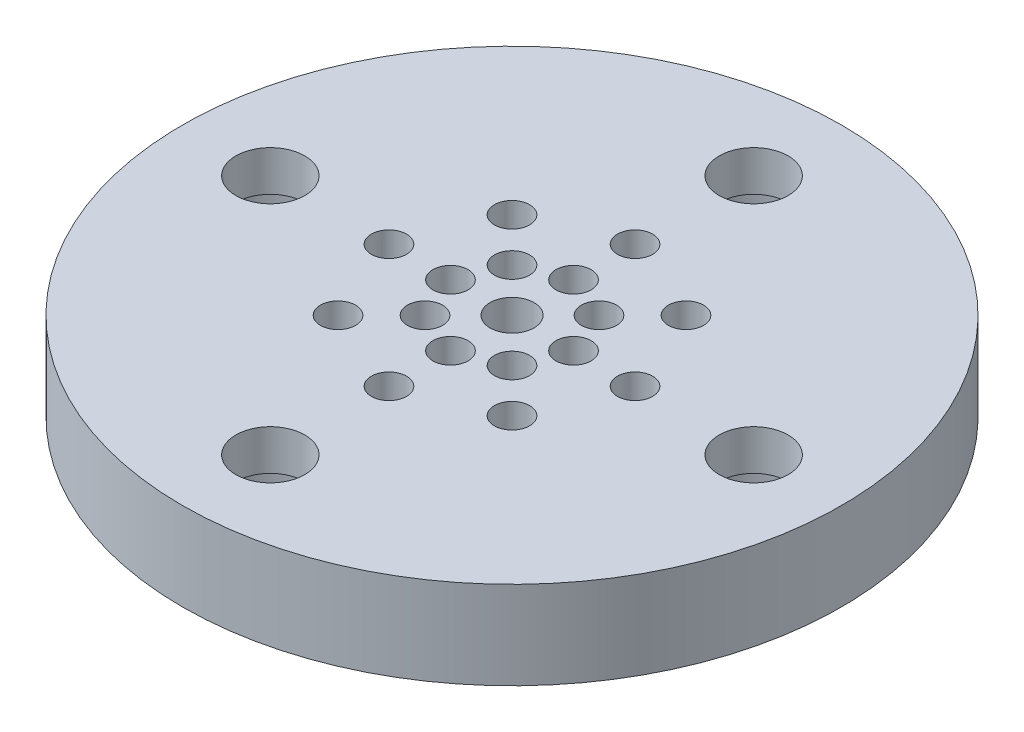
SolidWorks part; units mm, degrees
ref_plane "Front Plane" through (0, 0, 0) normal (0, 0, 1) x (1, 0, 0)
ref_plane "Top Plane" through (0, 0, 0) normal (0, 1, 0) x (1, 0, 0)
ref_plane "Right Plane" through (0, 0, 0) normal (1, 0, 0) x (0, 0, -1)
sketch "Sketch1" plane through (0, 0, 0) normal (0, 1, 0) x (1, 0, 0)
  circle A1 centre (0, 0) radius 50.8
  dimension "D1" = 101.6
extrude "Boss-Extrude1" add sketch "Sketch1" along normal blind 25.4
sketch "Sketch2" plane through (0, 0, 0) normal (0, -1, 0) x (1, 0, 0)
  circle A0 centre (0, 0) radius 50.8
  circle A1 centre (0, 0) radius 69.85
  dimension "D1" = 139.7
extrude "Boss-Extrude2" add sketch "Sketch2" against normal blind 12.7
sketch "Sketch3" plane through (0, 0, 0) normal (0, -1, 0) x (1, 0, 0)
  circle A0 centre (0, 0) radius 49.53
  circle A1 centre (0, 0) radius 47.625
  dimension "D1" = 99.06
  dimension "D2" = 95.25
extrude "Cut-Extrude1" cut sketch "Sketch3" against normal blind 1.1176
sketch "Sketch4" plane through (0, 0, 0) normal (0, -1, 0) x (1, 0, 0)
  circle A0 centre (0, -59.9186) radius 3.175
  circle A1 centre (-42.3688, -42.3688) radius 3.175
  circle A2 centre (-59.9186, 0) radius 3.175
  circle A3 centre (-42.3688, 42.3688) radius 3.175
  circle A4 centre (0, 59.9186) radius 3.175
  circle A5 centre (42.3688, 42.3688) radius 3.175
  circle A6 centre (59.9186, 0) radius 3.175
  circle A7 centre (42.3688, -42.3688) radius 3.175
  point P35 (0, 0)
  dimension "D2" = 6.35
  dimension "D1" = 59.9186
  dimension "D3" = 8
extrude "Cut-Extrude2" cut sketch "Sketch4" against normal up to next
sketch "Sketch5" plane through (0, 25.4, 0) normal (0, 1, 0) x (1, 0, 0)
  circle A0 centre (0, 0) radius 11.43
  dimension "D1" = 22.86
extrude "Cut-Extrude3" cut sketch "Sketch5" against normal blind 19.05 from offset 0
sketch "Sketch6" plane through (0, 6.35, 0) normal (0, 1, 0) x (1, 0, 0)
  circle A0 centre (0, 0) radius 1.5875
  dimension "D1" = 3.175
extrude "Cut-Extrude4" cut sketch "Sketch6" against normal up to next
sketch "Sketch30" plane through (0, 0, 0) normal (1, 0, 0) x (0, 0, -1)
  line L0 (0, -28.0613) -> (0, 0) construction
sketch "Sketch42" plane through (0, 0, 0) normal (0, -1, 0) x (1, 0, 0)
  circle A0 centre (0, 0) radius 23.8125
  dimension "D1" = 47.625
extrude "Cut-Extrude9" cut sketch "Sketch42" against normal blind 30.48 flip side to cut
sketch "Sketch43" plane through (0, 25.4, 0) normal (0, 1, 0) x (1, 0, 0)
  circle A0 centre (0, 0) radius 20.6375
extrude "Cut-Extrude10" cut sketch "Sketch43" against normal blind 19.05
hole_wizard "CBORE for #10 Binding Head Machine Screw1" positions "Sketch50" profile "Sketch51" counterbore size "#10" standard "ANSI Inch" end condition through all
sketch "Sketch50" plane through (0, 0, 0) normal (0, -1, 0) x (-1, 0, 0)
  line L0 (0, 0) -> (0, -25.4) construction
  line L2 (0, 0) -> (0, 25.4) construction
  line L4 (0, 0) -> (-25.4, 0) construction
  line L6 (0, 0) -> (25.4, 0) construction
  circle A0 centre (0, 0) radius 17.4625 construction
  point P0 (0, -17.4625)
  point P2 (-17.4625, 0)
  point P4 (17.4625, 0)
  point P6 (0, 17.4625)
  dimension "D1" = 34.925
sketch "Sketch51" plane through (0, 0, 17.4625) normal (1, 0, 0) x (0, 0, -1)
  line L0 (0, 0) -> (0, 25.4)
  line L1 (0, 25.4) -> (2.4892, 25.4)
  line L3 (2.4892, 25.4) -> (2.4892, 3.429)
  line L4 (2.4892, 3.429) -> (4.7625, 3.429)
  line L5 (4.7625, 3.429) -> (4.7625, 0)
  line L7 (4.7625, 0) -> (0, 0)
  line L11 (0, -6.35) -> (0, 107.95) construction
  dimension "Thru Hole Dia." = 4.9784
  dimension "Thru Hole Depth" = 25.4
  dimension "C'Bore Dia." = 9.525
  dimension "C'Bore Depth" = 3.429
sketch "Sketch52" plane through (0, 25.4, 0) normal (0, 1, 0) x (1, 0, 0)
  circle A0 centre (0, 0) radius 23.8125
  dimension "D1" = 47.625
extrude "Cut-Extrude11" cut sketch "Sketch52" against normal blind 19.05
sketch "Sketch53" plane through (0, 0, 0) normal (0, 0, 1) x (1, 0, 0)
  line L0 (0, 0) -> (0, 27.3338) construction
sketch "Sketch54" plane through (0, 6.35, 0) normal (0, 1, 0) x (1, 0, 0)
  circle A0 centre (0, -4.445) radius 1.27
  dimension "D1" = 2.54
  dimension "D2" = 4.445
extrude "Cut-Extrude12" cut sketch "Sketch54" against normal blind 6.35
pattern_circular "CirPattern1" count 8 over 360 about axis through (0, 0, 0) along (0, 1, 0) of "Cut-Extrude12"
sketch "Sketch55" plane through (0, 6.35, 0) normal (0, 1, 0) x (1, 0, 0)
  circle A0 centre (0, -8.89) radius 1.27
  dimension "D1" = 2.54
  dimension "D2" = 8.89
extrude "Cut-Extrude13" cut sketch "Sketch55" against normal blind 6.35
pattern_circular "CirPattern2" count 8 over 360 about axis through (0, 0, 0) along (0, 1, 0) of "Cut-Extrude13"
